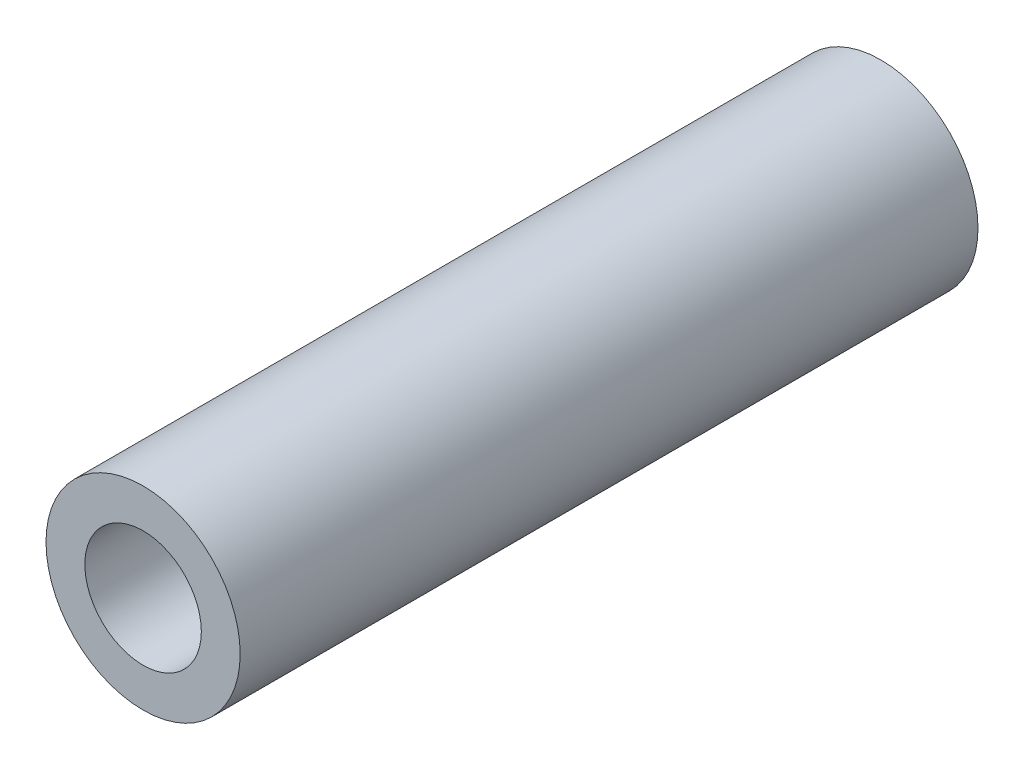
SolidWorks part; units mm, degrees
ref_plane "Plano frontal" through (0, 0, 0) normal (0, 0, 1) x (1, 0, 0)
ref_plane "Plano superior" through (0, 0, 0) normal (0, 1, 0) x (1, 0, 0)
ref_plane "Plano direito" through (0, 0, 0) normal (1, 0, 0) x (0, 0, -1)
sketch "Esboço1" plane through (0, 0, 0) normal (0, 0, 1) x (1, 0, 0)
  circle A0 centre (0, 0) radius 5
  circle A1 centre (0, 0) radius 3
  dimension "D1" = 6
  dimension "D2" = 10
extrude "Ressalto-extrusão1" add sketch "Esboço1" along normal blind 38
